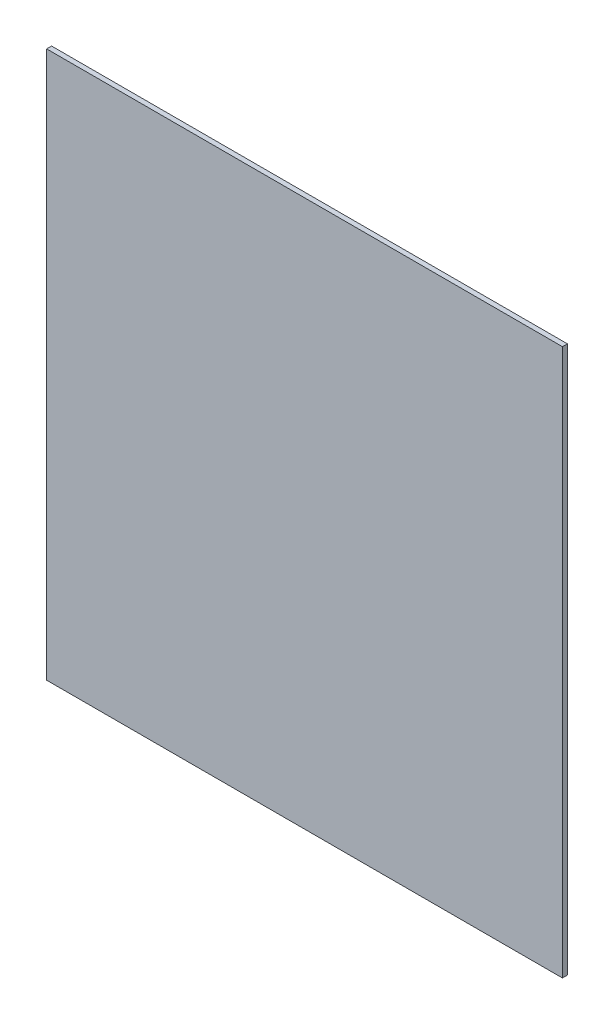
SolidWorks part; units mm, degrees
material "ABS PC"
ref_plane "Front Plane" through (0, 0, 0) normal (0, 0, 1) x (1, 0, 0)
ref_plane "Top Plane" through (0, 0, 0) normal (0, 1, 0) x (1, 0, 0)
ref_plane "Right Plane" through (0, 0, 0) normal (1, 0, 0) x (0, 0, -1)
sketch "Sketch1" plane through (0, 0, 0) normal (0, 0, 1) x (1, 0, 0)
  line L0 (-67.04, -71.5962) -> (-67.04, -97.0282) construction
  line L1 (-67.04, -91.3291) -> (-80.28, -91.3291)
  line L2 (-67.04, -91.3291) -> (-67.04, -77.2954)
  line L3 (-67.04, -77.2954) -> (-80.28, -77.2954)
  line L4 (-80.28, -91.3291) -> (-80.28, -77.2954)
  line L5 (-67.04, -91.3291) -> (-80.28, -77.2954) construction
  line L6 (-67.04, -77.2954) -> (-80.28, -91.3291) construction
  line L7 (-80.28, -97.0282) -> (-80.28, -71.5962) construction
  line L8 (-79.2162, -84.3122) -> (-68.1037, -84.3122) construction
  line L9 (-79.2162, -89.7574) -> (-79.2162, -78.8671) construction
  line L10 (-68.1037, -78.8671) -> (-68.1037, -89.7574) construction
  line L11 (-79.2162, -84.3122) -> (-80.28, -84.3122) construction
  line L12 (-73.66, -91.3291) -> (-73.66, -90.2654) construction
  line L13 (-68.6117, -90.2654) -> (-78.7082, -90.2654) construction
  point P4 (-73.66, -84.3122)
extrude "Boss-Extrude1" add sketch "Sketch1" along normal blind 0.127
